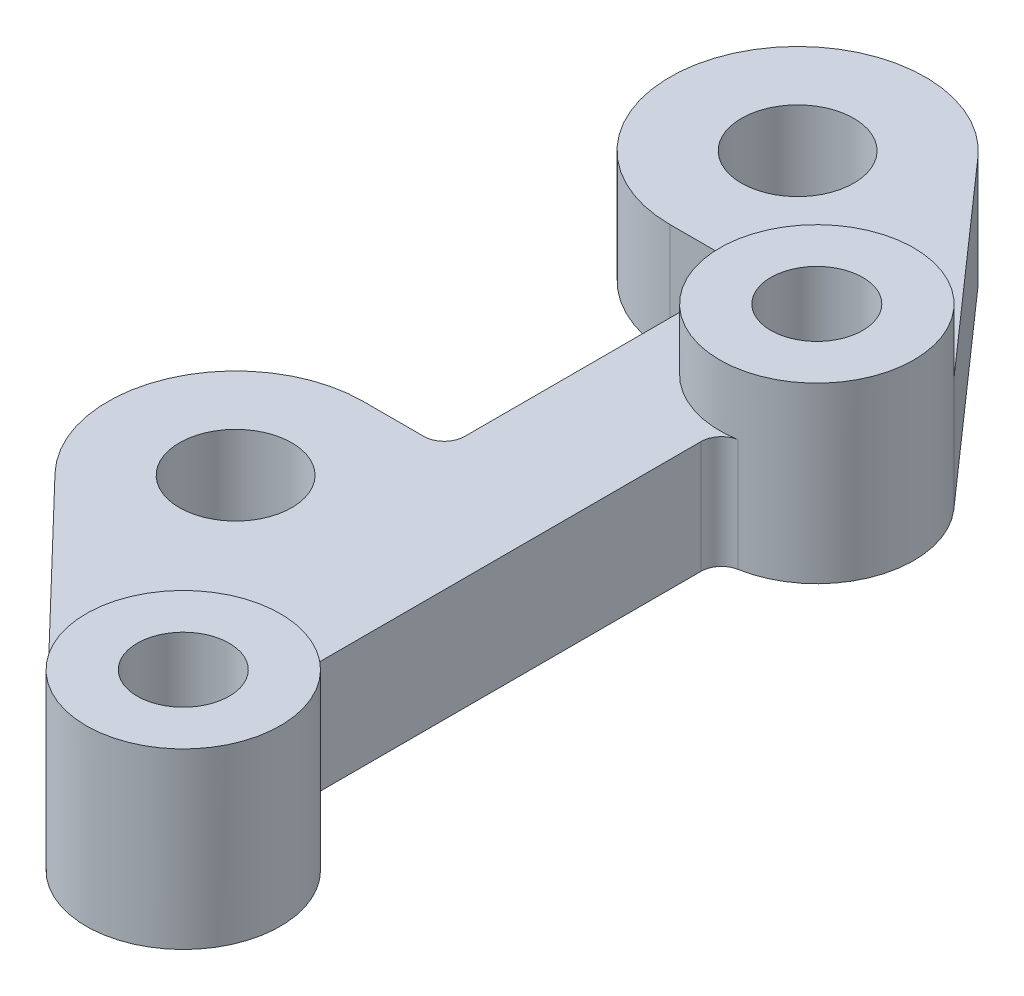
SolidWorks part; units mm, degrees
ref_plane "Face" through (0, 0, 0) normal (0, 0, 1) x (1, 0, 0)
ref_plane "Dessus" through (0, 0, 0) normal (0, 1, 0) x (1, 0, 0)
ref_plane "Droite" through (0, 0, 0) normal (1, 0, 0) x (0, 0, -1)
sketch "Esquisse1" plane through (0, 0, 0) normal (0, 1, 0) x (1, 0, 0)
  line L0 (0, -11.8101) -> (0, 83.5814) construction
  line L1 (-19.9205, -13.2) -> (-19.9205, 83.5926) construction
  line L2 (-28.9305, 16.3792) -> (-6.8476, -6.5849)
  line L3 (-19.9205, 25.0435) -> (0, 0) construction
  line L4 (-19.9205, 80.0435) -> (0, 62) construction
  line L5 (0, 50.6752) -> (0, 11.3248)
  line L6 (-12, 65.5435) -> (-12, 39.5435)
  line L7 (7.1237, 68.2852) -> (-10.5472, 88.3134)
  line L8 (-19.9205, 67.5435) -> (-14, 67.5435)
  line L9 (-19.9205, 37.5435) -> (-14, 37.5435)
  circle A0 centre (0, 0) radius 4.5
  circle A1 centre (-19.9205, 25.0435) radius 5.5
  circle A2 centre (0, 62) radius 4.5
  circle A3 centre (-19.9205, 80.0435) radius 5.5
  arc A4 (-6.8476, -6.5849) -> (1.6522, 9.3552) centre (0, 0) ccw
  arc A5 (-28.9305, 16.3792) -> (-19.9205, 37.5435) centre (-19.9205, 25.0435) cw
  arc A6 (-19.9205, 67.5435) -> (-10.5472, 88.3134) centre (-19.9205, 80.0435) cw
  arc A7 (1.6522, 52.6448) -> (7.1237, 68.2852) centre (0, 62) ccw
  arc A8 (1.6522, 9.3552) -> (0, 11.3248) centre (2, 11.3248) cw
  arc A9 (-14, 37.5435) -> (-12, 39.5435) centre (-14, 39.5435) ccw
  arc A10 (-14, 67.5435) -> (-12, 65.5435) centre (-14, 65.5435) cw
  arc A11 (0, 50.6752) -> (1.6522, 52.6448) centre (2, 50.6752) cw
  point P14 (0, 0)
  point P20 (-19.9345, 83.5814)
  point P24 (0, 9.5)
  point P32 (0, 52.5)
  dimension "D1" = 9
  dimension "D2" = 9
  dimension "D6" = 11
  dimension "D8" = 11
  dimension "D9" = 9.5
  dimension "D10" = 12.5
  dimension "D11" = 9.5
  dimension "D12" = 12.5
  dimension "D14" = 2
  dimension "D15" = 2
  dimension "D16" = 2
  dimension "D3" = 62
  dimension "D4" = 32
  dimension "D5" = 38.5
  dimension "D7" = 55
  dimension "D13" = 12
extrude "Boss.-Extru.1" add sketch "Esquisse1" along normal blind 11
sketch "Esquisse3" plane through (0, 11, 0) normal (0, 1, 0) x (1, 0, 0)
  circle A0 centre (0, 0) radius 4.5
  circle A1 centre (0, 0) radius 9.5
  circle A2 centre (0, 62) radius 4.5
  circle A3 centre (0, 62) radius 9.5
extrude "Boss.-Extru.3" add sketch "Esquisse3" along normal blind 6
